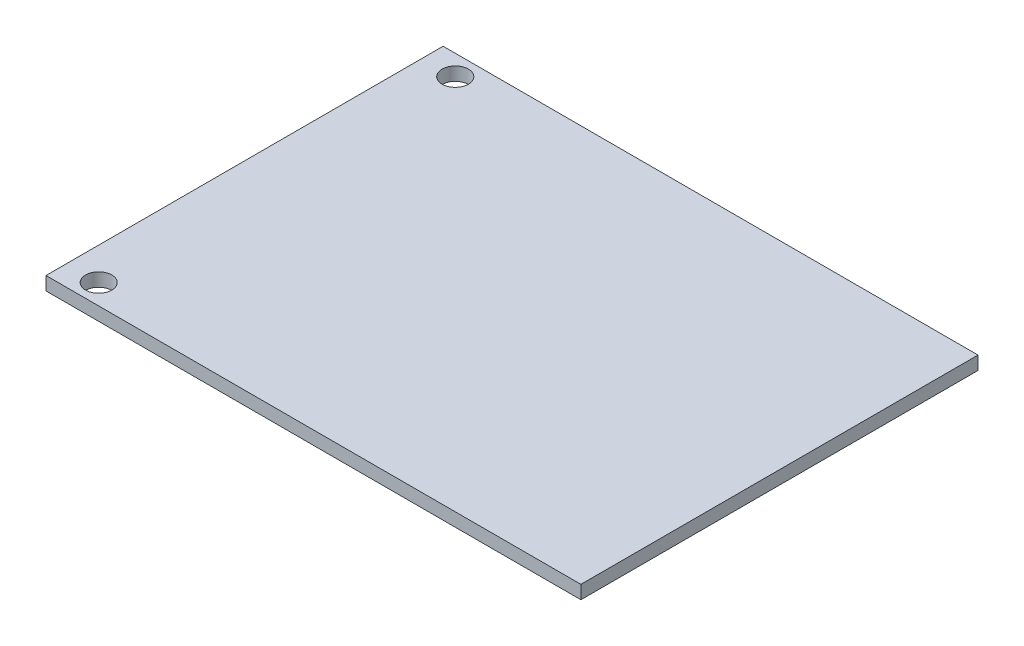
SolidWorks part; units mm, degrees
ref_plane "Front Plane" through (0, 0, 0) normal (0, 0, 1) x (1, 0, 0)
ref_plane "Top Plane" through (0, 0, 0) normal (0, 1, 0) x (1, 0, 0)
ref_plane "Right Plane" through (0, 0, 0) normal (1, 0, 0) x (0, 0, -1)
sketch "Sketch1" plane through (0, 0, 0) normal (0, 1, 0) x (1, 0, 0)
  line L1 (-33, -24.5) -> (33, -24.5)
  line L2 (-33, -24.5) -> (-33, 24.5)
  line L3 (-33, 24.5) -> (33, 24.5)
  line L4 (33, -24.5) -> (33, 24.5)
  line L5 (-33, -24.5) -> (33, 24.5) construction
  line L6 (-33, 24.5) -> (33, -24.5) construction
  point P0 (0, 0)
  dimension "D1" = 49
  dimension "D2" = 66
extrude "Boss-Extrude1" add sketch "Sketch1" along normal blind 1.651
sketch "Sketch2" plane through (0, 1.651, 0) normal (0, 1, 0) x (1, 0, 0)
  line L0 (-29, 22) -> (-29, -22) construction
  line L1 (-33, 24.5) -> (-33, -24.5) construction
  circle A0 centre (-29, 22) radius 1.62
  circle A1 centre (-29, -22) radius 1.62
  point P4 (-29, 0)
  dimension "D1" = 3.24
  dimension "D2" = 44
  dimension "D3" = 4
extrude "Cut-Extrude1" cut sketch "Sketch2" against normal through all
